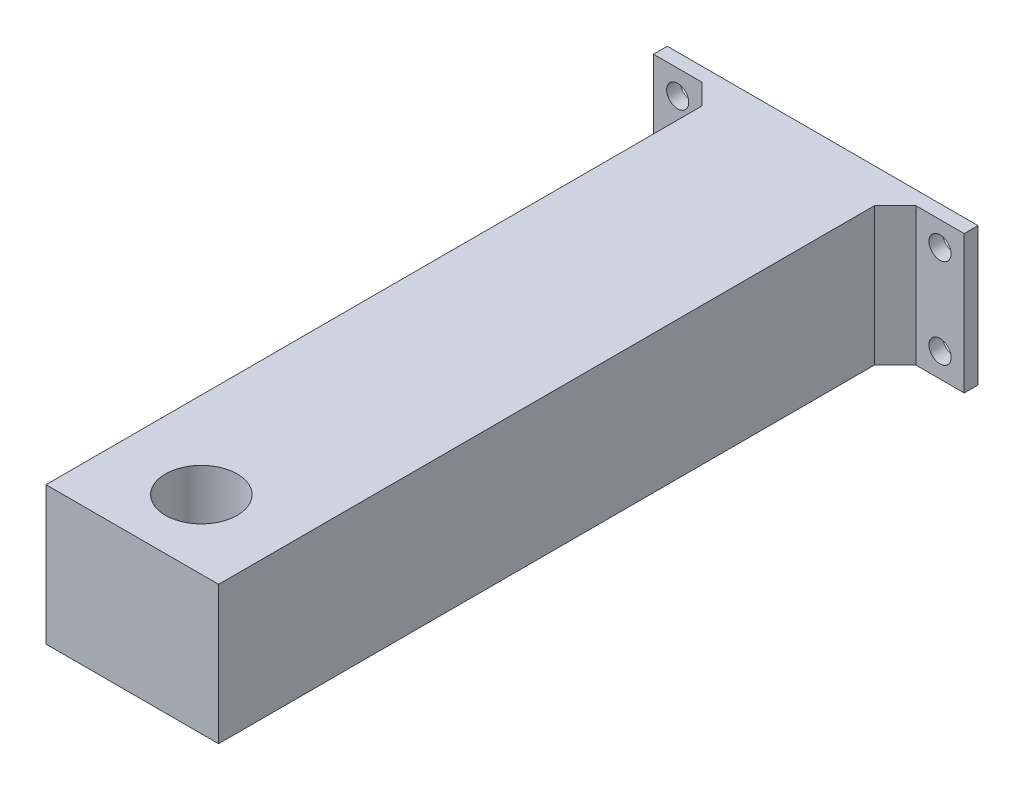
SolidWorks part; units mm, degrees
ref_plane "正面" through (0, 0, 0) normal (0, 0, 1) x (1, 0, 0)
ref_plane "平面" through (0, 0, 0) normal (0, 1, 0) x (1, 0, 0)
ref_plane "右側面" through (0, 0, 0) normal (1, 0, 0) x (0, 0, -1)
sketch "ｽｹｯﾁ1" plane through (0, 0, 0) normal (0, 0, 1) x (1, 0, 0)
  line L1 (-12.7289, 5.1915) -> (12.2711, 5.1915)
  line L2 (-12.7289, 5.1915) -> (-12.7289, -14.8085)
  line L3 (-12.7289, -14.8085) -> (12.2711, -14.8085)
  line L4 (12.2711, 5.1915) -> (12.2711, -14.8085)
  dimension "D1" = 25
  dimension "D2" = 20
extrude "ﾎﾞｽ - 押し出し1" add sketch "ｽｹｯﾁ1" along normal blind 100
sketch "ｽｹｯﾁ2" plane through (0, 5.1915, 0) normal (0, 1, 0) x (1, 0, 0)
  line L0 (-0.2289, -90) -> (12.2711, -90) construction
  line L1 (12.2711, -100) -> (12.2711, 0) construction
  line L2 (-0.2289, -90) -> (-12.7289, -90) construction
  line L3 (-12.7289, -100) -> (-12.7289, 0) construction
  line L4 (12.2711, -100) -> (-12.7289, -100) construction
  circle A0 centre (-0.2289, -90) radius 5.2
  dimension "D1" = 10.4
  dimension "D2" = 10
extrude "ｶｯﾄ - 押し出し1" cut sketch "ｽｹｯﾁ2" against normal blind 8
sketch "ｽｹｯﾁ3" plane through (12.2711, 0, 0) normal (1, 0, 0) x (0, 0, -1)
  line L0 (-100, -14.8085) -> (0, -14.8085) construction
  line L1 (0, 5.1915) -> (-2, 5.1915)
  line L2 (0, 5.1915) -> (0, -14.8085)
  line L3 (0, -14.8085) -> (-2, -14.8085)
  line L4 (-2, 5.1915) -> (-2, -14.8085)
  dimension "D2" = 2
extrude "ﾎﾞｽ - 押し出し2" add sketch "ｽｹｯﾁ3" along normal blind 10
sketch "ｽｹｯﾁ5" plane through (0, 5.1915, 0) normal (0, 1, 0) x (1, 0, 0)
  line L0 (12.2711, -5) -> (15.2711, -2)
  line L1 (12.2711, -100) -> (12.2711, -2) construction
  line L2 (22.2711, -2) -> (12.2711, -2) construction
  line L3 (15.2711, -2) -> (12.2711, -2)
  line L4 (12.2711, -2) -> (12.2711, -5)
  dimension "D1" = 3
extrude "ﾎﾞｽ - 押し出し3" add sketch "ｽｹｯﾁ5" against normal through all
sketch "ｽｹｯﾁ6" plane through (0, 0, 2) normal (0, 0, 1) x (1, 0, 0)
  line L0 (18.7711, 1.6915) -> (15.2711, 1.6915) construction
  line L1 (15.2711, -14.8085) -> (15.2711, 5.1915) construction
  line L2 (18.7711, 1.6915) -> (22.2711, 1.6915) construction
  line L3 (22.2711, 5.1915) -> (22.2711, -14.8085) construction
  line L4 (18.7711, -11.3085) -> (15.2711, -11.3085) construction
  line L5 (18.7711, -11.3085) -> (22.2711, -11.3085) construction
  line L6 (18.7711, -11.3085) -> (18.7711, -14.8085) construction
  line L7 (22.2711, -14.8085) -> (15.2711, -14.8085) construction
  line L8 (18.7711, 1.6915) -> (18.7711, 5.1915) construction
  line L9 (22.2711, 5.1915) -> (15.2711, 5.1915) construction
  circle A0 centre (18.7711, 1.6915) radius 1.6
  circle A1 centre (18.7711, -11.3085) radius 1.6
  point P10 (0, 0)
  dimension "D1" = 3.2
  dimension "D2" = 3.2
extrude "ｶｯﾄ - 押し出し2" cut sketch "ｽｹｯﾁ6" against normal through all
sketch "ｽｹｯﾁ7" plane through (-12.7289, 0, 0) normal (-1, 0, 0) x (0, 0, 1)
  line L0 (100, 5.1915) -> (0, 5.1915) construction
  line L1 (0, -14.8085) -> (2, -14.8085)
  line L2 (0, -14.8085) -> (0, 5.1915)
  line L3 (0, 5.1915) -> (2, 5.1915)
  line L4 (2, -14.8085) -> (2, 5.1915)
  point P7 (1, -14.8085)
  dimension "D1" = 2
extrude "ﾎﾞｽ - 押し出し4" add sketch "ｽｹｯﾁ7" along normal blind 10
sketch "ｽｹｯﾁ8" plane through (0, -14.8085, 0) normal (0, -1, 0) x (1, 0, 0)
  line L0 (-12.7289, 5) -> (-15.7289, 2)
  line L1 (-12.7289, 100) -> (-12.7289, 2) construction
  line L2 (-22.7289, 2) -> (-12.7289, 2) construction
  line L3 (-15.7289, 2) -> (-12.7289, 2)
  line L4 (-12.7289, 2) -> (-12.7289, 5)
  dimension "D1" = 3
extrude "ﾎﾞｽ - 押し出し5" add sketch "ｽｹｯﾁ8" against normal through all
sketch "ｽｹｯﾁ9" plane through (0, 0, 2) normal (0, 0, 1) x (1, 0, 0)
  line L0 (-19.2289, 1.6915) -> (-15.7289, 1.6915) construction
  line L1 (-15.7289, 5.1915) -> (-15.7289, -14.8085) construction
  line L2 (-19.2289, 1.6915) -> (-22.7289, 1.6915) construction
  line L3 (-22.7289, -14.8085) -> (-22.7289, 5.1915) construction
  line L4 (-19.2289, -11.3085) -> (-22.7289, -11.3085) construction
  line L5 (-19.2289, -11.3085) -> (-15.7289, -11.3085) construction
  line L6 (-19.2289, 1.6915) -> (-19.2289, 5.1915) construction
  line L7 (-22.7289, 5.1915) -> (-15.7289, 5.1915) construction
  line L8 (-19.2289, -11.3085) -> (-19.2289, -14.8085) construction
  line L9 (-22.7289, -14.8085) -> (-15.7289, -14.8085) construction
  circle A0 centre (-19.2289, -11.3085) radius 1.6
  circle A1 centre (-19.2289, 1.6915) radius 1.6
  dimension "D1" = 3.2
  dimension "D2" = 3.2
extrude "ｶｯﾄ - 押し出し3" cut sketch "ｽｹｯﾁ9" against normal through all
